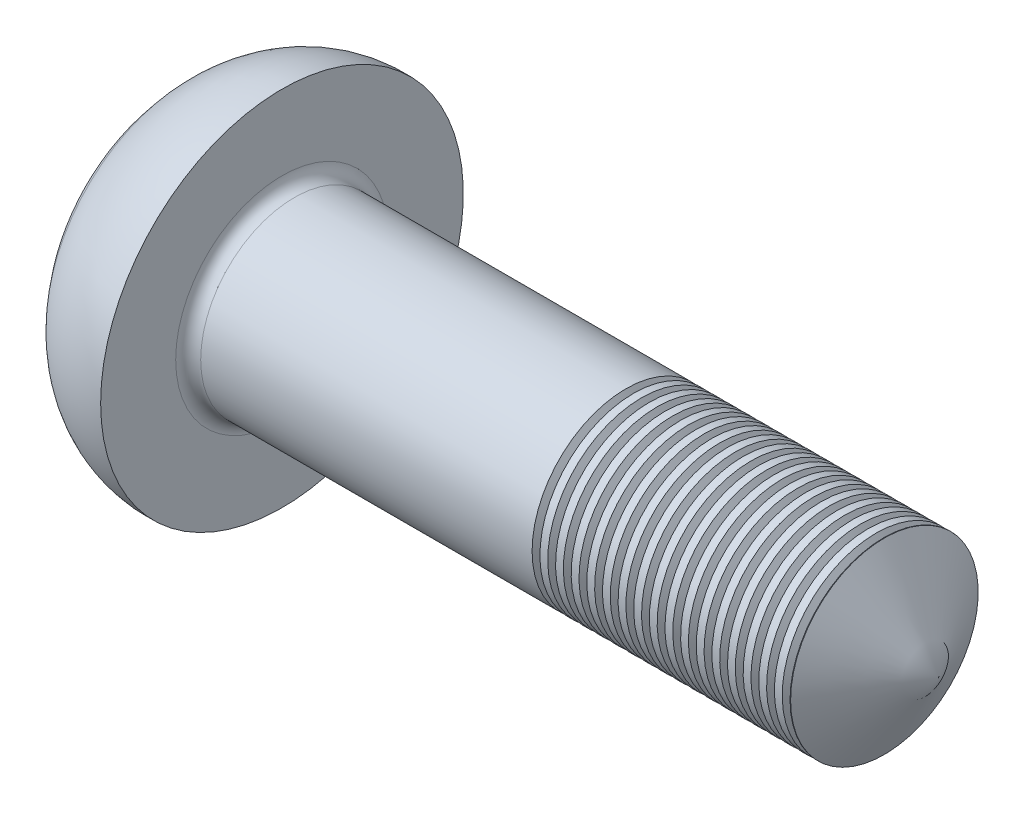
SolidWorks part; units mm, degrees
ref_plane "Front" through (0, 0, 0) normal (0, 0, 1) x (1, 0, 0)
ref_plane "Top" through (0, 0, 0) normal (0, 1, 0) x (1, 0, 0)
ref_plane "Right" through (0, 0, 0) normal (1, 0, 0) x (0, 0, -1)
sketch "Sketch1" plane through (0, 0, 0) normal (0, 1, 0) x (1, 0, 0)
  line L0 (-13.6293, 0) -> (11.3577, 0) construction
  line L1 (2.37, 1.5) -> (12.87, 1.5)
  line L2 (12.87, 1.5) -> (12.87, 0)
  line L3 (2.37, 1.5) -> (2.37, 2.9)
  line L4 (12.87, 0) -> (0, 0)
  arc A0 (2.37, 2.9) -> (0.8698, 2.2711) centre (2.2837, 1.002) ccw
  arc A1 (0, 0) -> (0.8698, 2.2711) centre (3.4, 0) cw
  dimension "r2" = 1.9
  dimension "r1" = 3.4
  dimension "d" = 3
  dimension "dk" = 5.8
  dimension "k" = 2.37
  dimension "l" = 10.5
revolve "Revolve1" add sketch "Sketch1" angle 360 about L0
cosmetic thread "ThreadCosmetic1" [suppressed] parameters "l0"=3.5, "dm"=2.75
fillet "Fillet2" radius 0.2 1 edges at (2.37, 0, 1.5)
sketch "Sketch4" plane through (0, 0, 0) normal (0, 1, 0) x (1, 0, 0)
  line L0 (4.7828, 0) -> (7.1391, 0) construction
  line L2 (13.6035, 0) -> (13.6035, 21)
  line L3 (13.6035, 21) -> (0.7456, 21)
  line L4 (0.7456, 21) -> (12.87, 0)
  line L5 (12.87, 0) -> (13.6035, 0)
  line L7 (12.87, -1.5) -> (12.87, 1.5) construction
  dimension "D1" = 60
  dimension "D2" = 0.7335
  dimension "D3" = 21
revolve "Cut-Revolve1" cut sketch "Sketch4" angle 360 about L0
sketch "Sketch2" plane through (0, 0, 0) normal (1, 0, 0) x (0, 0, -1)
  line L0 (-2.278, 0) -> (2.6944, 0) construction
  line L1 (0, -2.1234) -> (0, 2.1948) construction
  line L2 (-0.4625, 0.4625) -> (-1.85, 0.4625)
  line L3 (0.4625, -1.85) -> (-0.4625, -1.85)
  line L4 (0.4625, -1.85) -> (0.4625, -0.4625)
  line L5 (0.4625, 1.85) -> (-0.4625, 1.85)
  line L6 (-0.4625, -1.85) -> (-0.4625, -0.4625)
  line L7 (1.85, 0.4625) -> (0.4625, 0.4625)
  line L8 (1.85, 0.4625) -> (1.85, -0.4625)
  line L9 (1.85, -0.4625) -> (0.4625, -0.4625)
  line L10 (-1.85, 0.4625) -> (-1.85, -0.4625)
  line L11 (-0.4625, 0.4625) -> (-0.4625, 1.85)
  line L12 (-0.4625, -0.4625) -> (-1.85, -0.4625)
  line L13 (0.4625, 0.4625) -> (0.4625, 1.85)
  point P19 (-0.4625, 0.4625)
  point P22 (0.4625, 0.4625)
  point P27 (-0.4625, -0.4625)
  dimension "m" = 3.7
  dimension "D2" = 3.7
  dimension "D3" = 0.925
  dimension "D4" = 0.925
ref_plane "Plane1" through (2.62, 0, 0) normal (1, 0, 0) x (0, 0, -1)
sketch "Sketch5" plane through (2.62, 0, 0) normal (1, 0, 0) x (0, 0, -1)
  point P0 (0, 0)
loft "Cut-Loft1" cut profiles "Sketch5", "Sketch2"
sketch "Sketch6" plane through (0, 0, 0) normal (0, 0, 1) x (1, 0, 0)
  line L0 (7.87, 1.7) -> (7.995, 1.7)
  line L1 (7.995, 1.7) -> (7.995, 1.5)
  line L2 (7.995, 1.5) -> (7.9325, 1.3917)
  line L3 (7.87, 1.5) -> (7.9325, 1.3917)
  line L4 (7.87, 1.7) -> (7.87, 1.5)
  line L5 (10.7743, 0) -> (0, 0) construction
  line L6 (7.87, 1.5) -> (7.995, 1.5) construction
  line L7 (7.9325, 1.5) -> (7.9325, 1.3917) construction
  line L8 (12.004, 1.5) -> (2.57, 1.5) construction
  point P5 (7.9325, 1.7)
  dimension "D1" = 0.2
  dimension "D2" = 0.125
  dimension "D3" = 5
revolve "Cut-Revolve10" cut sketch "Sketch6" angle 360 about L5
pattern_linear "LPattern10" count 20 spacing 0.25 along (1, 0, 0) of "Cut-Revolve10"
equation "\"D4@Sketch2\" = \"D3@Sketch2\""
equation "\"D2@Sketch2\" = \"m@Sketch2\""
equation "\"D3@Sketch2\" = \"m@Sketch2\" / 4"
equation "\"D2@Sketch6\" = (  \"d@Sketch1\" - \"dm@ThreadCosmetic1\" )  / 2"
equation "\"D3@Sketch6\" = \"l0@ThreadCosmetic1\" + \"d@Sketch1\" / 2"
equation "\"D3@LPattern10\" = \"D2@Sketch6\" *2"
equation "\"D1@LPattern10\" = \"D3@Sketch6\" / \"D3@LPattern10\""
